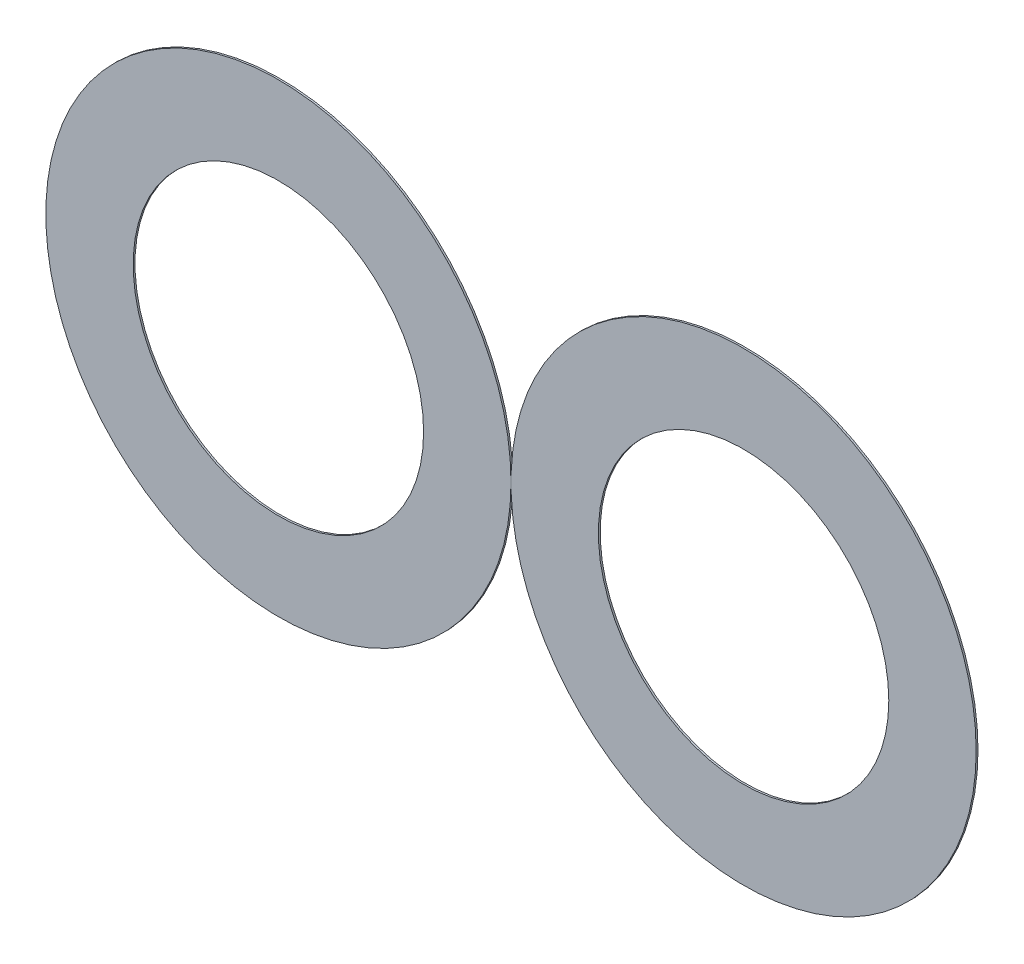
SolidWorks part; units mm, degrees
ref_plane "Alzado" through (0, 0, 0) normal (0, 0, 1) x (1, 0, 0)
ref_plane "Planta" through (0, 0, 0) normal (0, 1, 0) x (1, 0, 0)
ref_plane "Vista lateral" through (0, 0, 0) normal (1, 0, 0) x (0, 0, -1)
sketch "Model" plane through (0, 0, 0) normal (0, 0, 1) x (1, 0, 0)
  circle A0 centre (14.8206, 16.6) radius 12.8267
  circle A1 centre (40.474, 16.6) radius 12.8267
  circle A2 centre (14.8206, 16.6) radius 8.0078
  circle A3 centre (40.474, 16.6) radius 8.0078
extrude "Saliente-Extruir1" add sketch "Model" along normal blind 0.1 contours A0 A2 | A1 A3
